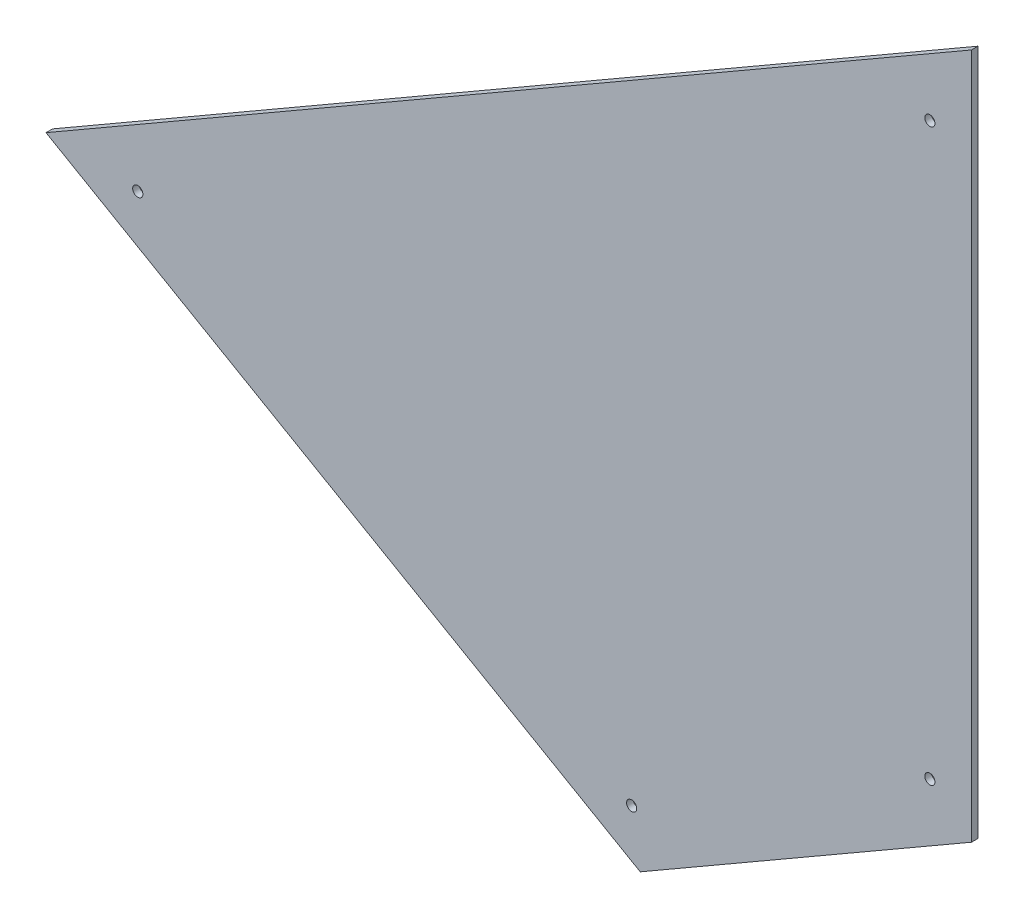
SolidWorks part; units mm, degrees
material "Акрил (Средняя-высокая ударопрочность)"
ref_plane "Спереди" through (0, 0, 0) normal (0, 0, 1) x (1, 0, 0)
ref_plane "Сверху" through (0, 0, 0) normal (0, 1, 0) x (1, 0, 0)
ref_plane "Справа" through (0, 0, 0) normal (1, 0, 0) x (0, 0, -1)
sketch "Эскиз3" plane through (0, 0, 0) normal (0, 0, 1) x (1, 0, 0)
  line L0 (0, -209.3174) -> (-101.0359, -267.6556)
  line L1 (-101.0359, -267.6556) -> (-282.3181, -163.0107)
  line L2 (-282.3181, -163.0107) -> (0, 0)
  line L3 (0, 0) -> (0, -209.3174)
extrude "Бобышка-Вытянуть1" add sketch "Эскиз3" along normal blind 2
sketch "Эскиз4" plane through (0, 0, 0) normal (0, 0, -1) x (-1, 0, 0)
  circle A0 centre (254.3244, -164.526) radius 1.55
  circle A2 centre (103.6642, -251.4944) radius 1.55
  circle A4 centre (12.6827, -198.9616) radius 1.55
  circle A6 centre (12.6827, -25.0018) radius 1.55
extrude "Вырез-Вытянуть1" cut sketch "Эскиз4" against normal blind 2
